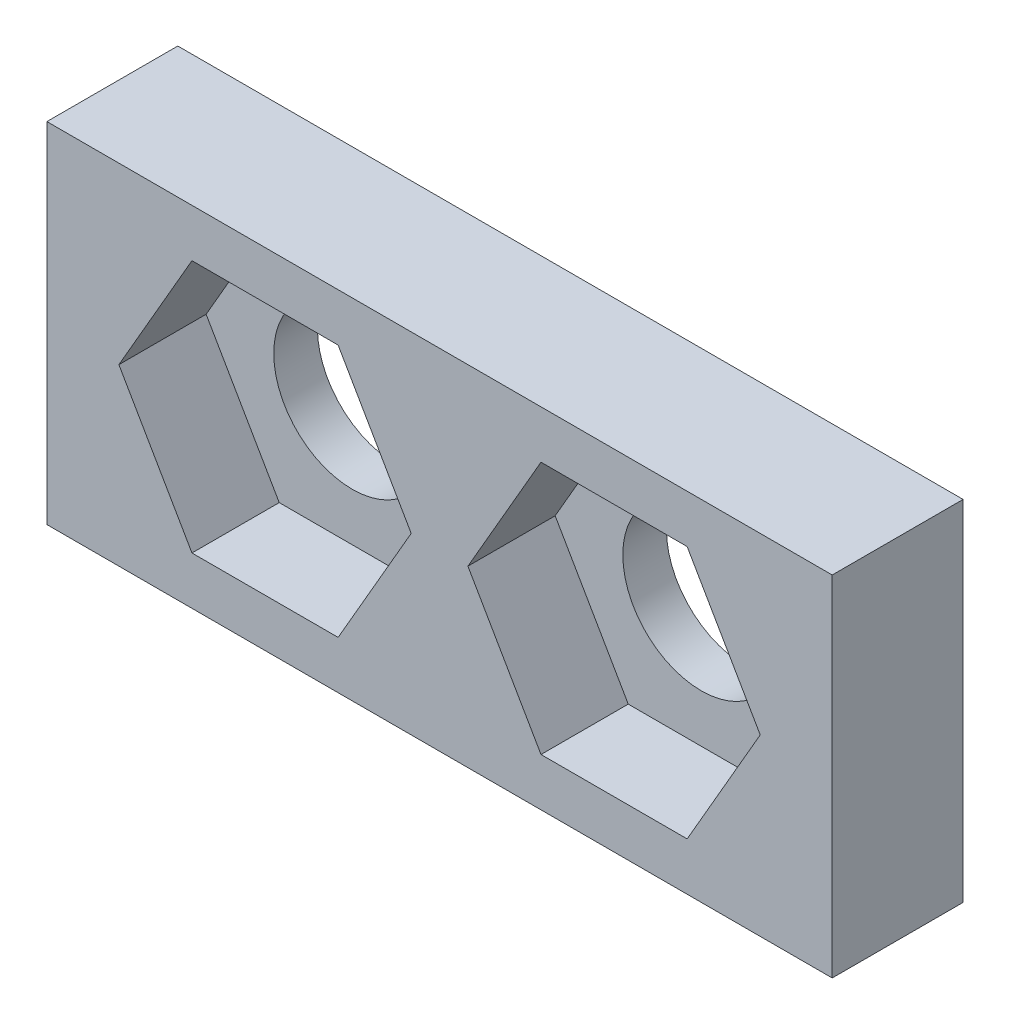
SolidWorks part; units mm, degrees
ref_plane "前视基准面" through (0, 0, 0) normal (0, 0, 1) x (1, 0, 0)
ref_plane "上视基准面" through (0, 0, 0) normal (0, 1, 0) x (1, 0, 0)
ref_plane "右视基准面" through (0, 0, 0) normal (1, 0, 0) x (0, 0, -1)
ref_plane "基准面4" through (0, 0, 0) normal (0, 0, -1) x (-1, 0, 0)
sketch "草图1" plane through (0, 0, 0) normal (0, 0, -1) x (-1, 0, 0)
  line L0 (-9, 296) -> (9, 296)
  line L1 (9, 296) -> (9, 304)
  line L2 (9, 304) -> (-9, 304)
  line L3 (-9, 304) -> (-9, 296)
extrude "凸台-拉伸1" add sketch "草图1" against normal blind 3
sketch "草图2" plane through (0, 0, 3) normal (0, 0, 1) x (1, 0, 0)
  line L0 (-0.65, 300) -> (-2.325, 302.9012)
  line L1 (-2.325, 302.9012) -> (-5.675, 302.9012)
  line L2 (-5.675, 302.9012) -> (-7.35, 300)
  line L3 (-7.35, 300) -> (-5.675, 297.0988)
  line L4 (-5.675, 297.0988) -> (-2.325, 297.0988)
  line L5 (-2.325, 297.0988) -> (-0.65, 300)
extrude "切除-拉伸1" cut sketch "草图2" against normal blind 2
sketch "草图3" plane through (0, 0, 3) normal (0, 0, 1) x (1, 0, 0)
  line L0 (5.675, 297.0988) -> (7.35, 300)
  line L1 (7.35, 300) -> (5.675, 302.9012)
  line L2 (5.675, 302.9012) -> (2.325, 302.9012)
  line L3 (2.325, 302.9012) -> (0.65, 300)
  line L4 (0.65, 300) -> (2.325, 297.0988)
  line L5 (2.325, 297.0988) -> (5.675, 297.0988)
extrude "切除-拉伸2" cut sketch "草图3" against normal blind 2
hole_wizard "Ø3.6 (3.6) 直径孔1" positions "草图5" profile "草图4" hole size "Ø3.6" standard "ANSI Metric"
sketch "草图5" plane through (0, 0, 0) normal (0, 0, -1) x (-1, 0, 0)
  point P0 (-4, 300)
  point P1 (4, 300)
sketch "草图4" plane through (4, 300, 0) normal (1, 0, 0) x (0, 1, 0)
  line L0 (0, 0) -> (0, 3)
  line L1 (0, 3) -> (1.8, 3)
  line L2 (1.8, 3) -> (1.8, 0)
  line L5 (1.8, 0) -> (0, 0)
  line L11 (0, -6.35) -> (0, 107.95) construction
  dimension "通孔孔直径" = 3.6
  dimension "通孔孔深度" = 3
